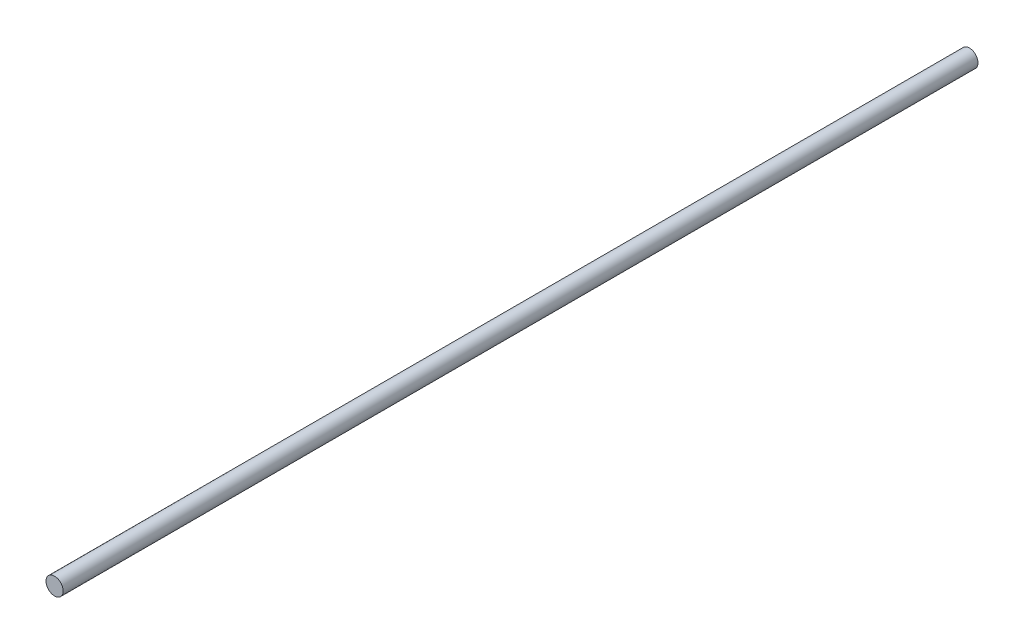
SolidWorks part; units mm, degrees
ref_plane "Front Plane" through (0, 0, 0) normal (0, 0, 1) x (1, 0, 0)
ref_plane "Top Plane" through (0, 0, 0) normal (0, 1, 0) x (1, 0, 0)
ref_plane "Right Plane" through (0, 0, 0) normal (1, 0, 0) x (0, 0, -1)
sketch "Sketch1" plane through (0, 0, 0) normal (0, 0, 1) x (1, 0, 0)
  circle A0 centre (0, 0) radius 4
  dimension "D1" = 8
extrude "Boss-Extrude1" add sketch "Sketch1" along normal blind 426
